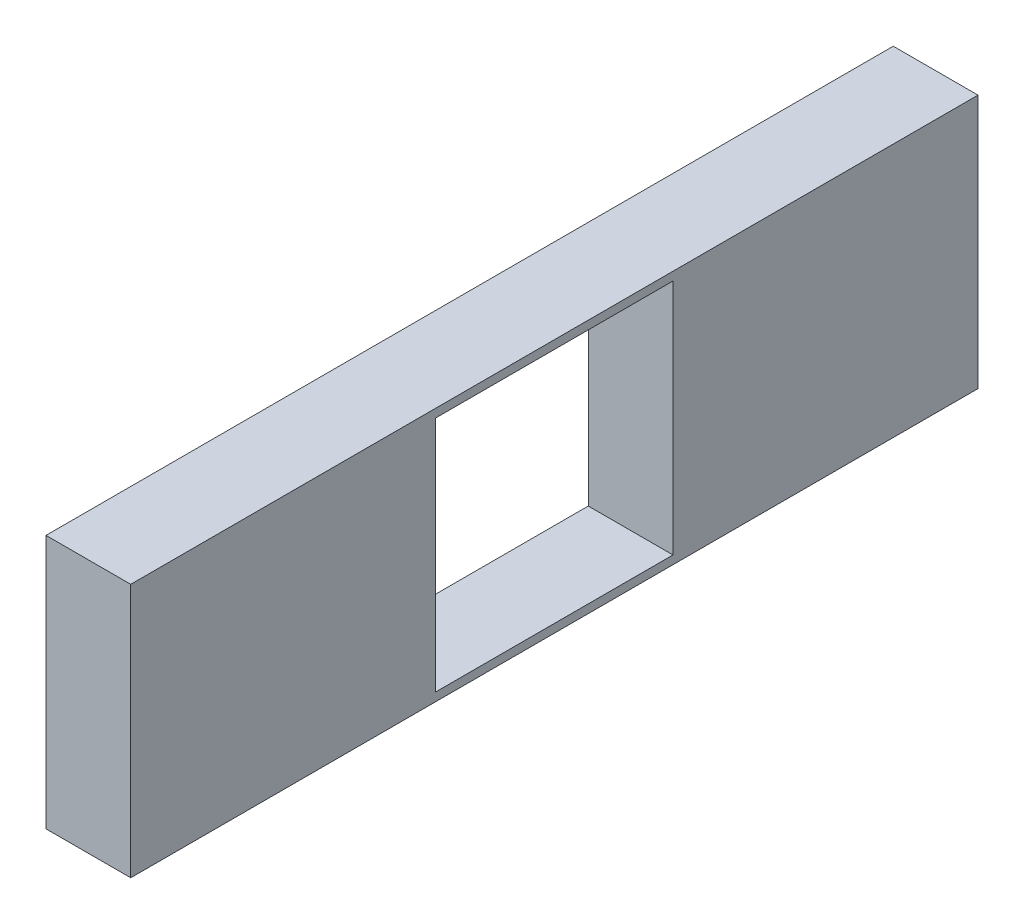
SolidWorks part; units mm, degrees
ref_plane "Front Plane" through (0, 0, 0) normal (0, 0, 1) x (1, 0, 0)
ref_plane "Top Plane" through (0, 0, 0) normal (0, 1, 0) x (1, 0, 0)
ref_plane "Right Plane" through (0, 0, 0) normal (1, 0, 0) x (0, 0, -1)
sketch "Sketch1" plane through (0, 0, 0) normal (1, 0, 0) x (0, 0, -1)
  line L0 (18, 15) -> (50, 15)
  line L1 (0, 0) -> (50, 0)
  line L2 (0, 0) -> (0, 15)
  line L3 (0, 15) -> (18, 15)
  line L4 (50, 0) -> (50, 15)
  line L10 (32, 14.5) -> (18, 14.5)
  line L11 (32, 14.5) -> (32, 0.5)
  line L12 (32, 0.5) -> (18, 0.5)
  line L13 (18, 14.5) -> (18, 0.5)
  dimension "D1" = 50
  dimension "D2" = 18
  dimension "Height" = 15
  dimension "D3" = 14
  dimension "D4" = 14
  dimension "D5" = 0.5
extrude "Boss-Extrude1" add sketch "Sketch1" along normal blind 5
